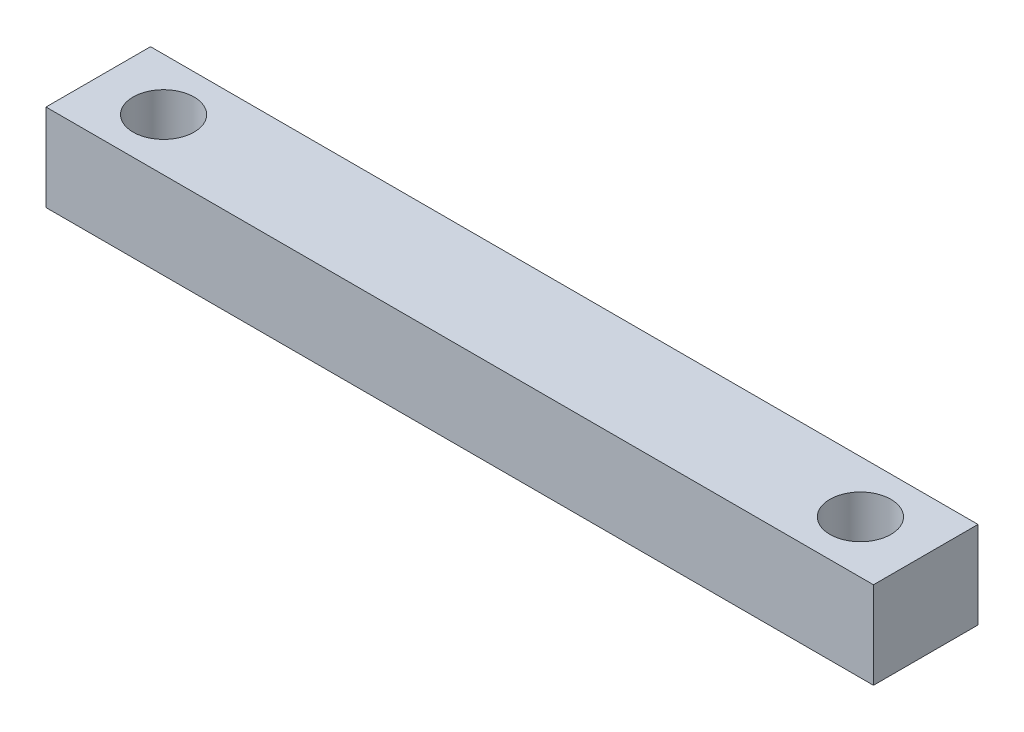
SolidWorks part; units mm, degrees
ref_plane "Front Plane" through (0, 0, 0) normal (0, 0, 1) x (1, 0, 0)
ref_plane "Top Plane" through (0, 0, 0) normal (0, 1, 0) x (1, 0, 0)
ref_plane "Right Plane" through (0, 0, 0) normal (1, 0, 0) x (0, 0, -1)
sketch "Sketch1" plane through (0, 0, 0) normal (0, 1, 0) x (1, 0, 0)
  line L0 (-23.75, 0) -> (23.75, 0) construction
  line L1 (-23.75, -3) -> (23.75, -3)
  line L2 (-23.75, -3) -> (-23.75, 3)
  line L3 (-23.75, 3) -> (23.75, 3)
  line L4 (23.75, -3) -> (23.75, 3)
  line L5 (-23.75, -3) -> (23.75, 3) construction
  line L6 (-23.75, 3) -> (23.75, -3) construction
  circle A0 centre (-20, 0) radius 1.75
  circle A1 centre (20, 0) radius 1.75
  point P0 (0, 0)
  point P12 (-24.4486, 4.2921)
  dimension "D1" = 3.5
  dimension "D2" = 40
  dimension "D3" = 20
  dimension "D5" = 3
  dimension "D4" = 3.75
extrude "Boss-Extrude1" add sketch "Sketch1" along normal blind 5
